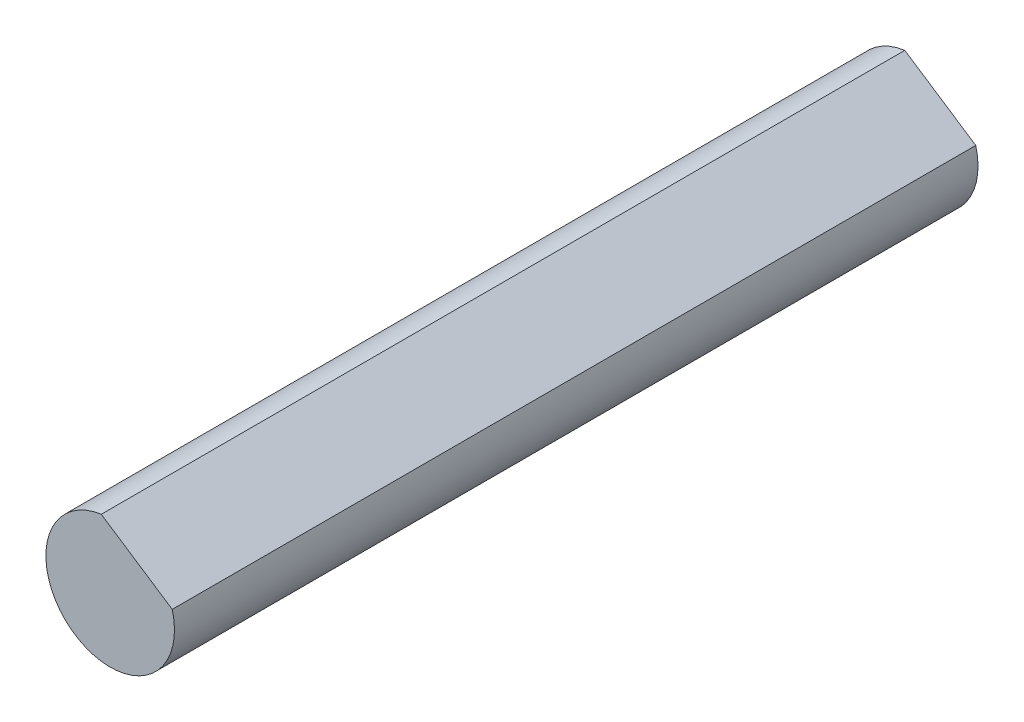
SolidWorks part; units mm, degrees
ref_plane "Front Plane" through (0, 0, 0) normal (0, 0, 1) x (1, 0, 0)
ref_plane "Top Plane" through (0, 0, 0) normal (0, 1, 0) x (1, 0, 0)
ref_plane "Right Plane" through (0, 0, 0) normal (1, 0, 0) x (0, 0, -1)
sketch "Sketch1" plane through (0, 0, 0) normal (0, 0, 1) x (1, 0, 0)
  line L0 (-0.2772, 1.9807) -> (1.9305, 0.5226)
  arc A0 (-0.2772, 1.9807) -> (1.9305, 0.5226) centre (0, 0) ccw
  dimension "D1" = 4
  dimension "D2" = 1.5
extrude "Boss-Extrude1" add sketch "Sketch1" along normal blind 25
